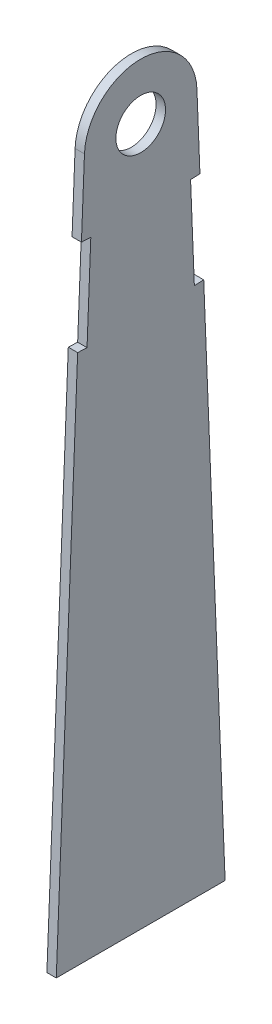
SolidWorks part; units mm, degrees
material "AISI 4130 Steel, annealed at 865C"
ref_plane "X-Y Datum" through (0, 0, 0) normal (0, 0, 1) x (1, 0, 0)
ref_plane "X-Z Datum" through (0, 0, 0) normal (0, 1, 0) x (1, 0, 0)
ref_plane "Y-Z Datum" through (0, 0, 0) normal (1, 0, 0) x (0, 0, -1)
sketch "Sketch1" plane through (0, 0, 0) normal (1, 0, 0) x (0, 0, -1)
  line L0 (0, -118.0251) -> (-14.2875, -118.0251)
  line L1 (-14.2875, -118.0251) -> (-9.5173, 0.3834)
  line L2 (0, -118.0251) -> (14.2875, -118.0251)
  line L3 (14.2875, -118.0251) -> (9.5173, 0.3834)
  line L4 (0, -118.0251) -> (0, 0) construction
  line L5 (-10.6675, -28.1684) -> (-9.0813, -28.2323)
  line L10 (-10.6675, -28.1684) -> (-10.0285, -12.3063)
  line L11 (-9.0813, -28.2323) -> (-8.4423, -12.3702)
  line L12 (-10.0285, -12.3063) -> (-8.4423, -12.3702)
  line L13 (10.6675, -28.1684) -> (10.0285, -12.3063)
  line L14 (10.6675, -28.1684) -> (9.0813, -28.2323)
  line L15 (10.0285, -12.3063) -> (8.4423, -12.3702)
  line L16 (9.0813, -28.2323) -> (8.4423, -12.3702)
  arc A0 (9.5173, 0.3834) -> (-9.5173, 0.3834) centre (0, 0) ccw
  dimension "D1" = 9.525
  dimension "D2" = 14.2875
  dimension "D3" = 14.2875
  dimension "D4" = 118.0251
  dimension "D5" = 1.5875
  dimension "D6" = 15.875
  dimension "D7" = 12.7
  dimension "D8" = 12.7
extrude "Boss-Extrude1" add sketch "Sketch1" along normal blind 1.5875
hole_wizard "M8 Clearance Hole1" positions "Sketch2" profile "Sketch3" hole size "M8" standard "ANSI Metric" end condition through all
sketch "Sketch2" plane through (1.5875, 0, 0) normal (1, 0, 0) x (0, 0, -1)
  point P0 (0, 0)
sketch "Sketch3" plane through (1.5875, 0, 0) normal (0, 1, 0) x (0, 0, -1)
  line L0 (0, 0) -> (0, 1.5875)
  line L1 (0, 1.5875) -> (4.2, 1.5875)
  line L2 (4.2, 1.5875) -> (4.2, 0)
  line L5 (4.2, 0) -> (0, 0)
  line L11 (0, -6.35) -> (0, 107.95) construction
  dimension "Thru Hole Dia." = 8.4
  dimension "Thru Hole Depth" = 1.5875
sketch "Sketch4" plane through (1.5875, 0, 0) normal (1, 0, 0) x (0, 0, -1)
  line L2 (10.0285, -12.3063) -> (9.5173, 0.3834) construction
  line L3 (-10.0285, -12.3063) -> (-9.5173, 0.3834) construction
  line L5 (9.6977, -4.0943) -> (9.5173, 0.3834)
  line L6 (-9.6977, -4.0943) -> (-9.5173, 0.3834)
  arc A3 (9.5173, 0.3834) -> (-9.5173, 0.3834) centre (0, 0) ccw construction
  arc A4 (9.5173, 0.3834) -> (-9.5173, 0.3834) centre (0, 0) ccw
  ellipse E0 centre (0, -4.7625) end of major axis (0, 7.9375) minor radius 9.7111 (9.6977, -4.0943) -> (-9.6977, -4.0943) ccw
  point P7 (0, 7.9375)
  dimension "D1" = 7.9375
  dimension "D2" = 4.7625
extrude "Cut-Extrude1" [suppressed] cut sketch "Sketch4" against normal through all
equation "\"D8@Sketch1\"=\"D7@Sketch1\""
